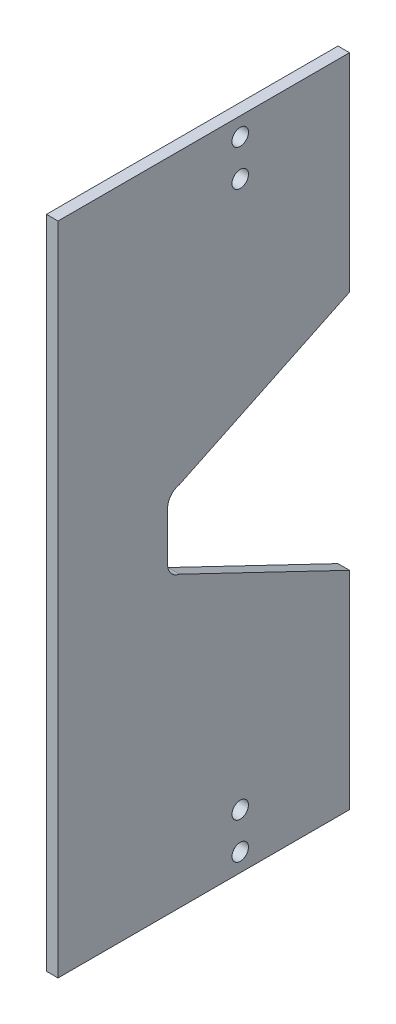
SolidWorks part; units mm, degrees
material "ABS"
ref_plane "前视基准面" through (0, 0, 0) normal (0, 0, 1) x (1, 0, 0)
ref_plane "上视基准面" through (0, 0, 0) normal (0, 1, 0) x (1, 0, 0)
ref_plane "右视基准面" through (0, 0, 0) normal (1, 0, 0) x (0, 0, -1)
ref_plane "基准面4" through (-0.7938, 0, 0) normal (-1, 0, 0) x (0, -1, 0)
sketch "草图1" plane through (-0.7938, 0, 0) normal (-1, 0, 0) x (0, -1, 0)
  line L1 (38.795, 5) -> (12.795, 5)
  line L2 (10.795, 3) -> (10.795, -13)
  line L5 (10.795, 3) -> (55.77, 3) construction
  line L6 (55.77, 3) -> (55.77, -5.0783) construction
  line L7 (55.77, 3) -> (55.77, 5) construction
  line L13 (38.795, 5) -> (72.745, 5)
  line L15 (100.745, 3) -> (100.745, -13)
  line L18 (72.745, 5) -> (98.745, 5)
  line L19 (55.77, 5) -> (55.77, -5.0783) construction
  line L20 (55.77, -5.0783) -> (55.77, -0.0391) construction
  line L21 (55.77, -0.0391) -> (65.77, -0.0391) construction
  line L22 (72.112, -14.1547) -> (62.1308, -0.0391) construction
  line L31 (13.295, -15) -> (13.295, -10) construction
  line L32 (13.295, 0) -> (13.295, -15) construction
  line L33 (18.295, 0) -> (18.295, -15) construction
  line L34 (18.295, -15) -> (18.295, -10) construction
  line L35 (93.245, 0) -> (93.245, -15) construction
  line L36 (93.245, -15) -> (93.245, -10) construction
  line L37 (93.245, -10) -> (98.245, -10) construction
  line L38 (55.77, -0.0391) -> (50.77, -0.0391)
  line L39 (55.77, -0.0391) -> (60.77, -0.0391)
  line L40 (12.795, -15) -> (47.795, -15)
  line L41 (98.745, -15) -> (63.745, -15)
  line L42 (50.77, -0.0391) -> (47.795, -15)
  line L43 (60.77, -0.0391) -> (63.745, -15)
  arc A2 (12.795, 5) -> (10.795, 3) centre (12.795, 3) ccw
  arc A3 (10.795, -13) -> (12.795, -15) centre (12.795, -13) ccw
  arc A12 (98.745, 5) -> (100.745, 3) centre (98.745, 3) cw
  arc A13 (100.745, -13) -> (98.745, -15) centre (98.745, -13) cw
  circle A17 centre (13.295, -10) radius 1.1303
  circle A18 centre (18.295, -10) radius 1.1303
  circle A19 centre (93.245, -10) radius 1.1303
  circle A20 centre (98.245, -10) radius 1.1303
extrude "凸台-拉伸1" add sketch "草图1" against normal blind 1.588
fillet "圆角1" radius 2 1 edges at (0.0003, -47.795, -15)
fillet "圆角2" radius 2 1 edges at (0.0002, -50.77, -0.0391)
fillet "圆角3" radius 2 1 edges at (0.0002, -60.77, -0.0391)
fillet "圆角4" radius 2 1 edges at (0.0003, -63.745, -15)
sketch "草图2" plane through (0.7942, 0, 0) normal (1, 0, 0) x (0, 0, -1)
  line L0 (-5, -55.77) -> (-15, -55.77) construction
  line L2 (-5, -98.745) -> (-5, -12.795) construction
  line L3 (-15, -55.77) -> (-15, -100.745) construction
  line L4 (-15, -100.745) -> (-3, -100.745) construction
  line L5 (-3, -100.745) -> (-3, -10.795) construction
  line L6 (-3, -10.795) -> (-15, -10.795) construction
  line L7 (-15, -10.795) -> (-15, -55.77) construction
  line L8 (-15, -10.795) -> (-3, -10.795)
  line L9 (-3, -10.795) -> (-3, -100.745)
  line L10 (-3, -100.745) -> (-15, -100.745)
  line L11 (-15, -100.745) -> (-15, -10.795)
  line L12 (15, -29.4743) -> (25, -29.4743) construction
  line L13 (15, -12.795) -> (15, -46.1535) construction
  line L14 (25, -29.4743) -> (25, -82.0657) construction
  line L15 (25, -82.0657) -> (15, -82.0657) construction
  line L16 (15, -65.3865) -> (15, -98.745) construction
  line L17 (15, -82.0657) -> (15, -100.745) construction
  line L18 (25, -82.0657) -> (25, -100.745) construction
  line L19 (25, -100.745) -> (13, -100.745) construction
  line L20 (13, -100.745) -> (-3, -100.745) construction
  line L21 (13, -100.745) -> (13, -10.795) construction
  line L22 (13, -10.795) -> (25, -10.795) construction
  line L23 (25, -10.795) -> (25, -29.4743) construction
  line L24 (1.6491, -50.4499) -> (13.3901, -48.1151) construction
  line L25 (13.3901, -48.1151) -> (25, -45.8065) construction
  line L26 (1.6491, -61.0901) -> (13.3901, -63.4249) construction
  line L27 (13.3901, -63.4249) -> (25, -65.7335) construction
  line L28 (13.3901, -48.1151) -> (25, -45.8065)
  line L29 (25, -45.8065) -> (25, -10.795)
  line L30 (25, -10.795) -> (13, -10.795)
  line L31 (13, -10.795) -> (13.3901, -48.1151)
  line L32 (13.3901, -63.4249) -> (25, -65.7335)
  line L33 (25, -65.7335) -> (25, -100.745)
  line L34 (25, -100.745) -> (13, -100.745)
  line L35 (13, -100.745) -> (13.3901, -63.4249)
  arc A0 (13, -100.745) -> (15, -98.745) centre (13, -98.745) ccw construction
extrude "凸台-拉伸2" add sketch "草图2" against normal blind 1.588
sketch "草图5" plane through (0.7942, 0, 0) normal (1, 0, 0) x (0, 0, -1)
  line L0 (25, -45.8065) -> (25, -10.795) construction
  line L1 (25, -10.795) -> (25, -28.3007) construction
  line L2 (25, -28.3007) -> (25, -45.8065) construction
  line L3 (25, -45.8065) -> (25, -37.0536) construction
  line L4 (25, -37.0536) -> (25, -41.43) construction
  line L5 (25, -41.43) -> (1.6491, -50.4499) construction
  line L7 (1.6491, -50.4499) -> (25, -45.8065)
  line L9 (0.0391, -55.77) -> (-15, -55.77) construction
  line L10 (0.0391, -52.4115) -> (0.0391, -59.1285) construction
  line L11 (-15, -10.795) -> (-15, -100.745) construction
  line L15 (25, -41.43) -> (25, -37.0536) construction
  line L16 (25, -37.0536) -> (25, -39.2418) construction
  line L17 (25, -39.2418) -> (1.6491, -50.4499) construction
  line L18 (1.6491, -50.4499) -> (25, -39.2418)
  line L19 (25, -39.2418) -> (25, -45.8065)
  line L20 (1.6491, -61.0901) -> (25, -72.2982)
  line L21 (1.6491, -61.0901) -> (25, -65.7335)
  line L22 (25, -72.2982) -> (25, -65.7335)
extrude "切除-拉伸1" cut sketch "草图5" against normal blind 10
